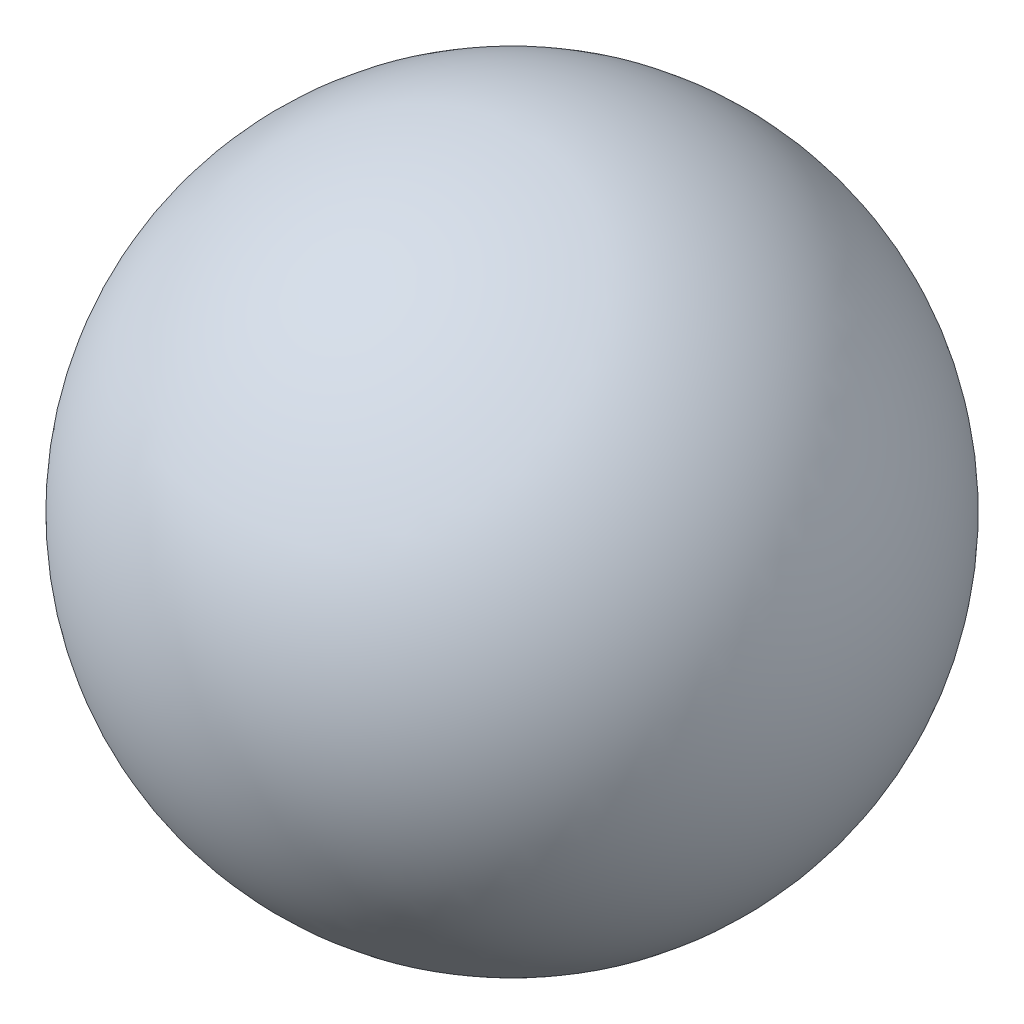
SolidWorks part; units mm, degrees
ref_plane "Front Plane" through (0, 0, 0) normal (1, 0, 0) x (0, 1, 0)
ref_plane "Top Plane" through (0, 0, 0) normal (0, 0, 1) x (0, 1, 0)
ref_plane "Right Plane" through (0, 0, 0) normal (0, 1, 0) x (-1, 0, 0)
sketch "Sketch1" plane through (0, 0, 0) normal (1, 0, 0) x (0, 1, 0)
  line L0 (0, 0) -> (20, 0) construction
  line L1 (-20, 0) -> (20, 0)
  arc A0 (20, 0) -> (-20, 0) centre (0, 0) ccw
  dimension "D1" = 40
revolve "Revolve1" add sketch "Sketch1" angle 360 about L0
